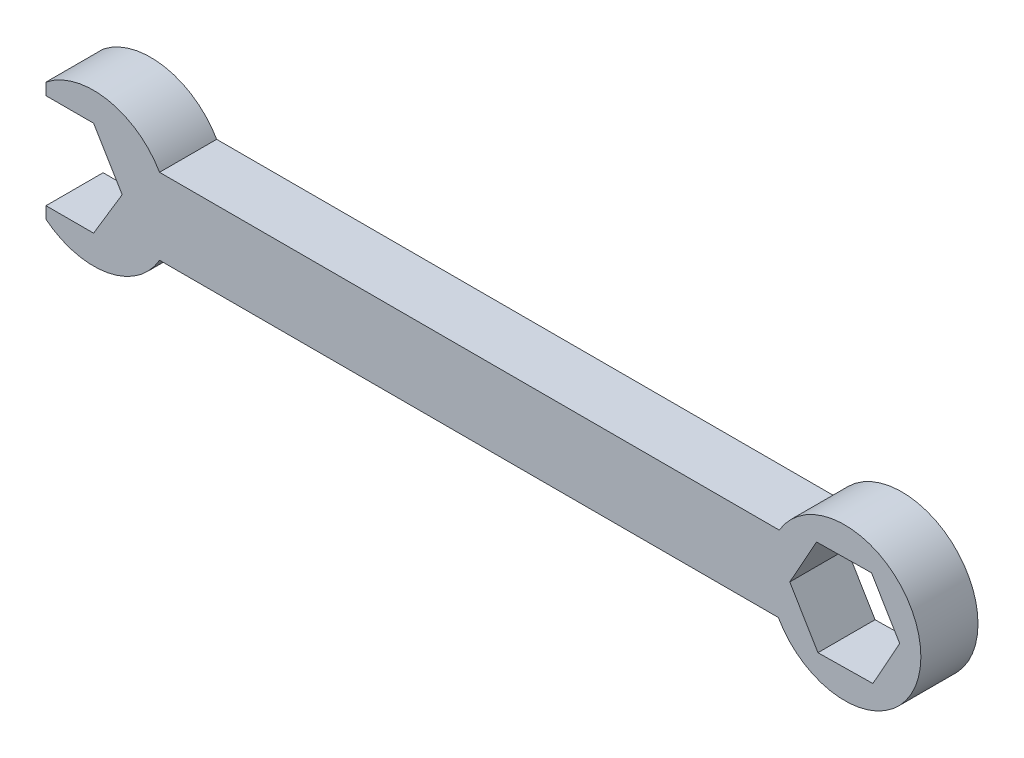
SolidWorks part; units mm, degrees
ref_plane "Front Plane" through (0, 0, 0) normal (0, 0, 1) x (1, 0, 0)
ref_plane "Top Plane" through (0, 0, 0) normal (0, 1, 0) x (1, 0, 0)
ref_plane "Right Plane" through (0, 0, 0) normal (1, 0, 0) x (0, 0, -1)
sketch "Sketch3" plane through (0, 0, 0) normal (0, 0, 1) x (1, 0, 0)
  line L1 (-10.16, 6.35) -> (-3.81, 6.35)
  line L3 (-10.16, -6.35) -> (-3.81, -6.35)
  line L4 (-3.81, 6.35) -> (0, 0)
  line L5 (0, 0) -> (-3.81, -6.35)
  line L6 (-10.16, 6.35) -> (-10.16, 7.9311)
  line L7 (-10.16, -6.35) -> (-10.16, -7.9311)
  line L10 (4.9888, 5.08) -> (87.658, 5.08)
  line L11 (4.9888, -5.08) -> (87.5388, -5.08)
  line L12 (100.153, -6.4001) -> (103.728, 0.0017)
  line L13 (103.728, 0.0017) -> (99.9713, 6.2986)
  line L14 (99.9713, 6.2986) -> (92.6398, 6.1937)
  line L15 (92.6398, 6.1937) -> (89.0648, -0.2081)
  line L16 (89.0648, -0.2081) -> (92.8214, -6.505)
  line L17 (92.8214, -6.505) -> (100.153, -6.4001)
  arc A0 (-10.16, -7.9311) -> (4.9888, -5.08) centre (-3.81, 0) ccw
  arc A1 (87.5388, -5.08) -> (87.658, 5.08) centre (96.3964, -0.1032) ccw
  arc A3 (4.9888, 5.08) -> (-10.16, 7.9311) centre (-3.81, 0) ccw
  point P13 (8.7175, 0)
  dimension "D1" = 6.35
  dimension "D2" = 12.7
extrude "Boss-Extrude2" add sketch "Sketch3" along normal blind 7.62
